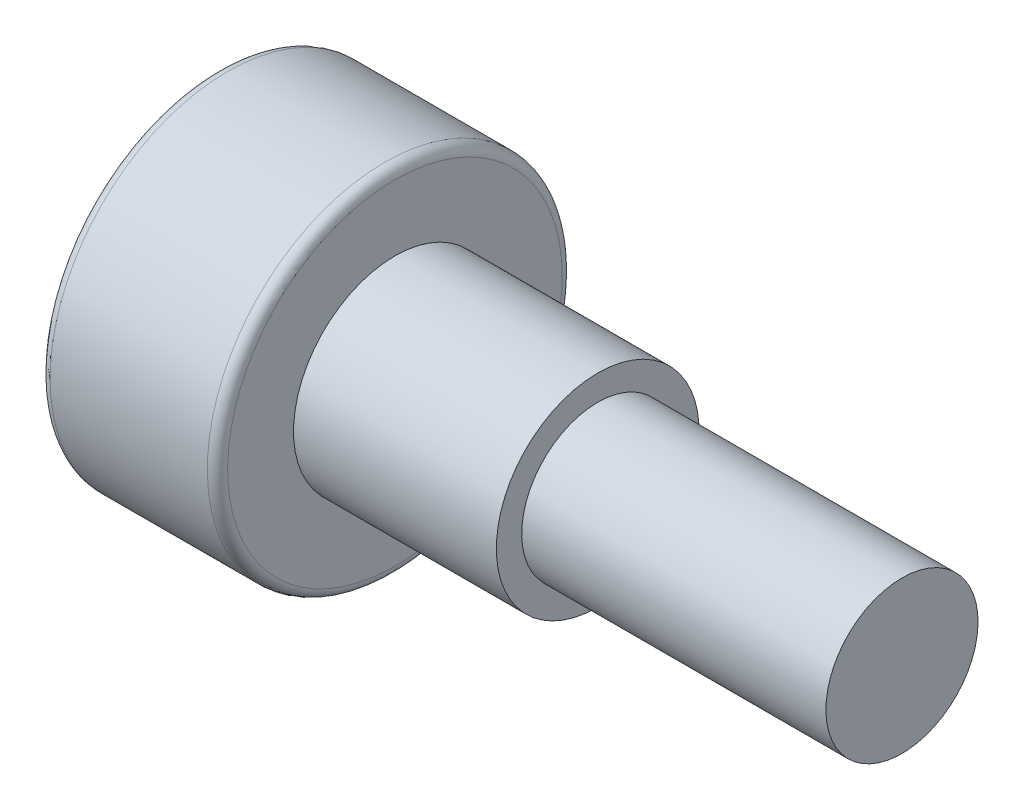
SolidWorks part; units mm, degrees
material "AISI 304"
ref_plane "前视基准面" through (0, 0, 0) normal (0, 0, 1) x (1, 0, 0)
ref_plane "上视基准面" through (0, 0, 0) normal (0, 1, 0) x (1, 0, 0)
ref_plane "右视基准面" through (0, 0, 0) normal (1, 0, 0) x (0, 0, -1)
sketch "草图1" plane through (0, 0, 0) normal (0, 0, 1) x (1, 0, 0)
  line L0 (0, 0) -> (0, 3.5)
  line L1 (0, 3.5) -> (3.5, 3.5)
  line L2 (3.5, 3.5) -> (3.5, 2)
  line L3 (3.5, 2) -> (7.5, 2)
  line L4 (7.5, 2) -> (7.5, 1.5)
  line L5 (7.5, 1.5) -> (13.5, 1.5)
  line L6 (13.5, 1.5) -> (13.5, 0)
  line L7 (13.5, 0) -> (0, 0) construction
  line L8 (0, 0) -> (13.5, 0)
  dimension "D1" = 7
  dimension "D2" = 4
  dimension "D3" = 3
  dimension "D4" = 3.5
  dimension "D5" = 4
  dimension "D6" = 6
revolve "旋转1" add sketch "草图1" angle 360 about L7
cosmetic thread "装饰螺纹线1" parameters "D2"=2.05
sketch "草图2" plane through (0, 0, 0) normal (-1, 0, 0) x (0, 0, 1)
  line L1 (1.5, 0.866) -> (0, 1.7321)
  line L2 (0, 1.7321) -> (-1.5, 0.866)
  line L3 (-1.5, 0.866) -> (-1.5, -0.866)
  line L4 (-1.5, -0.866) -> (0, -1.7321)
  line L5 (0, -1.7321) -> (1.5, -0.866)
  line L6 (1.5, -0.866) -> (1.5, 0.866)
  circle A0 centre (0, 0) radius 1.5 construction
  dimension "D1" = 3
extrude "切除-拉伸1" cut sketch "草图2" against normal blind 2
fillet "圆角1" radius 0.2 2 edges at (0, 3.5, 0) (3.5, 3.5, 0)
